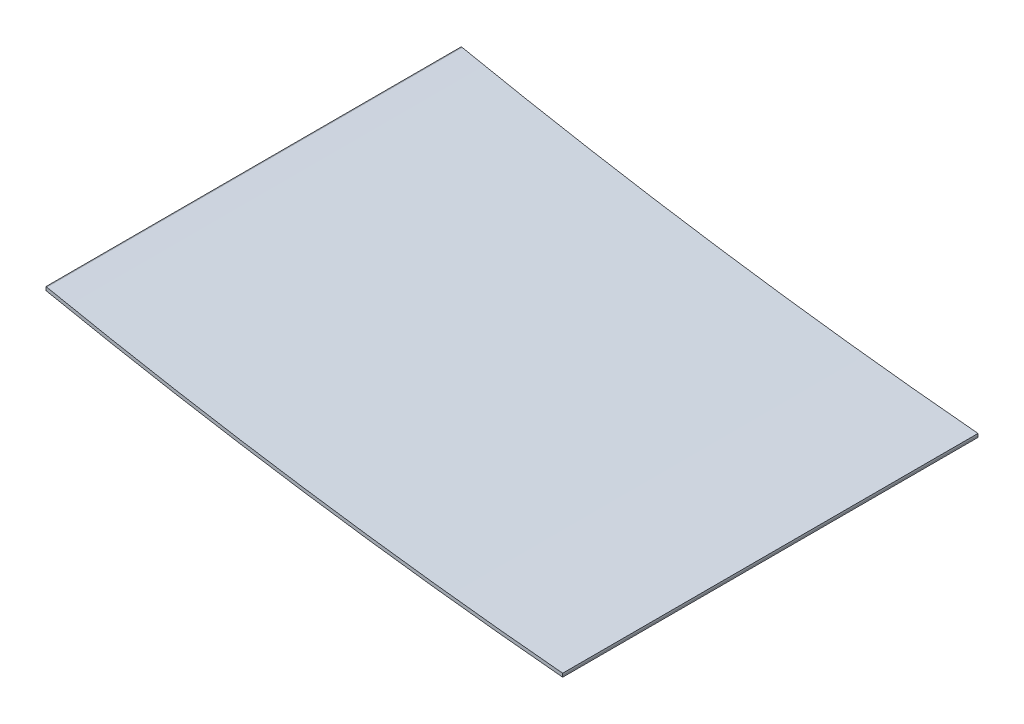
SolidWorks part; units mm, degrees
material "Acrylic (Medium-high impact)"
ref_plane "Front Plane" through (0, 0, 0) normal (0, 0, 1) x (1, 0, 0)
ref_plane "Top Plane" through (0, 0, 0) normal (0, 1, 0) x (1, 0, 0)
ref_plane "Right Plane" through (0, 0, 0) normal (1, 0, 0) x (0, 0, -1)
sketch "Sketch2" plane through (0, 0, 0) normal (0, 0, 1) x (1, 0, 0)
  line L0 (8671.1802, -15050.6764) -> (8671.1802, -15047.5703)
  line L1 (7924.7982, -14937.0078) -> (7924.7982, -14942.1121)
  line L2 (8671.1802, -15050.6764) -> (8671.1786, -15052.5911)
  line L3 (7925.8035, -14937.2142) -> (7924.7982, -14937.0078)
  arc A0 (7925.8035, -14937.2142) -> (8671.1802, -15047.5703) centre (9292.5752, -8278.0705) ccw
  arc A1 (5432.5752, -13879.9152) -> (9222.5752, -15080.6703) centre (9292.5752, -8278.0705) ccw construction
  arc A2 (7925.8035, -14937.2142) -> (8671.6353, -15047.612) centre (9292.5752, -8278.0705) ccw construction
  arc A4 (7924.7982, -14942.1121) -> (8671.1786, -15052.5911) centre (9292.5752, -8278.0705) ccw
  dimension "D1" = 5
extrude "Boss-Extrude1" add sketch "Sketch2" along normal blind 600
